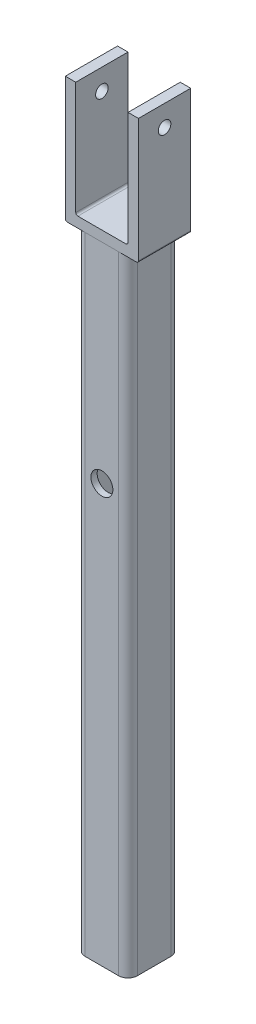
SolidWorks part; units mm, degrees
other "DetailItem2"
other "DetailItem3"
other "Weld Folder"
other "Weld Bead3"
other "Weld Bead2"
ref_plane "Front Plane" through (0, 0, 0) normal (0, 0, 1) x (1, 0, 0)
ref_plane "Top Plane" through (0, 0, 0) normal (0, 1, 0) x (1, 0, 0)
ref_plane "Right Plane" through (0, 0, 0) normal (1, 0, 0) x (0, 0, -1)
sketch "Sketch1" plane through (0, 0, 0) normal (0, 1, 0) x (1, 0, 0)
  line L15 (8, 12.5) -> (-8, 12.5)
  line L16 (12.5, 8) -> (12.5, -8)
  line L17 (8, -12.5) -> (-8, -12.5)
  line L18 (-12.5, 8) -> (-12.5, -8)
  line L19 (12.5, 12.5) -> (-12.5, -12.5) construction
  line L20 (12.5, -12.5) -> (-12.5, 12.5) construction
  line L21 (-6.5, 9.5) -> (6.5, 9.5)
  line L22 (-9.5, 6.5) -> (-9.5, -6.5)
  line L23 (-6.5, -9.5) -> (6.5, -9.5)
  line L24 (9.5, 6.5) -> (9.5, -6.5)
  line L25 (-9.5, 9.5) -> (9.5, -9.5) construction
  line L26 (-9.5, -9.5) -> (9.5, 9.5) construction
  arc A0 (-12.5, 8) -> (-8, 12.5) centre (-8, 8) cw
  arc A1 (8, 12.5) -> (12.5, 8) centre (8, 8) cw
  arc A2 (12.5, -8) -> (8, -12.5) centre (8, -8) cw
  arc A3 (-8, -12.5) -> (-12.5, -8) centre (-8, -8) cw
  arc A4 (-9.5, 6.5) -> (-6.5, 9.5) centre (-6.5, 6.5) cw
  arc A5 (6.5, 9.5) -> (9.5, 6.5) centre (6.5, 6.5) cw
  arc A6 (9.5, -6.5) -> (6.5, -9.5) centre (6.5, -6.5) cw
  arc A7 (-6.5, -9.5) -> (-9.5, -6.5) centre (-6.5, -6.5) cw
  point P0 (0, 0)
  point P6 (0, 0)
  dimension "D5" = 4.5
  dimension "D6" = 3
  dimension "D1" = 19
  dimension "D2" = 19
  dimension "D3" = 25
  dimension "D4" = 25
extrude "Boss-Extrude1" add sketch "Sketch1" along normal blind 300
sketch "Sketch2" plane through (0, 0, -12.5) normal (0, 0, -1) x (-1, 0, 0)
  line L0 (0, 0) -> (0, 200)
  line L1 (-8, 0) -> (8, 0) construction
  circle A0 centre (0, 200) radius 7.5
  dimension "D2" = 15
  dimension "D1" = 200
extrude "Cut-Extrude1" cut sketch "Sketch2" against normal blind 3 contours A0
sketch "Sketch3" plane through (0, 0, 12.5) normal (0, 0, 1) x (1, 0, 0)
  line L0 (0, 0) -> (0, 200)
  line L1 (-8, 0) -> (8, 0) construction
  circle A0 centre (0, 200) radius 5.25
  dimension "D1" = 10.5
extrude "Cut-Extrude2" cut sketch "Sketch3" against normal blind 3 contours A0
sketch "Sketch5" plane through (0, 300, 0) normal (0, 1, 0) x (1, 0, 0)
  line L1 (17.5, 12.5) -> (-17.5, 12.5)
  line L2 (17.5, 12.5) -> (17.5, -12.5)
  line L3 (17.5, -12.5) -> (-17.5, -12.5)
  line L4 (-17.5, 12.5) -> (-17.5, -12.5)
  line L5 (17.5, 12.5) -> (-17.5, -12.5) construction
  line L6 (17.5, -12.5) -> (-17.5, 12.5) construction
  point P0 (0, 0)
  dimension "D1" = 25
  dimension "D2" = 35
extrude "Boss-Extrude2" add sketch "Sketch5" along normal blind 60 separate body
sketch "Sketch6" plane through (0, 360, 0) normal (0, 1, 0) x (1, 0, 0)
sketch "Sketch7" plane through (0, 360, 0) normal (0, 1, 0) x (1, 0, 0)
  line L0 (17.5, 12.5) -> (-17.5, 12.5) construction
  line L1 (12.5, -12.5) -> (-12.5, -12.5)
  line L2 (12.5, -12.5) -> (12.5, 12.5)
  line L3 (12.5, 12.5) -> (-12.5, 12.5)
  line L4 (-12.5, -12.5) -> (-12.5, 12.5)
  line L5 (12.5, -12.5) -> (-12.5, 12.5) construction
  line L6 (12.5, 12.5) -> (-12.5, -12.5) construction
  point P0 (0, 0)
extrude "Cut-Extrude4" cut sketch "Sketch7" against normal blind 55
sketch "Sketch8" plane through (-17.5, 0, 0) normal (-1, 0, 0) x (0, 0, 1)
  line L0 (0, 360) -> (0, 350)
  line L1 (-12.5, 360) -> (12.5, 360) construction
  circle A0 centre (0, 350) radius 3
  dimension "D2" = 6
  dimension "D1" = 10
extrude "Cut-Extrude5" cut sketch "Sketch8" against normal blind 55 contours A0
fillet "Fillet1" radius 1 2 edges at (12.5, 305, 0) (-12.5, 305, 0)
fillet "Fillet2" radius 1 2 edges at (17.5, 300, 0) (-17.5, 300, 0)
